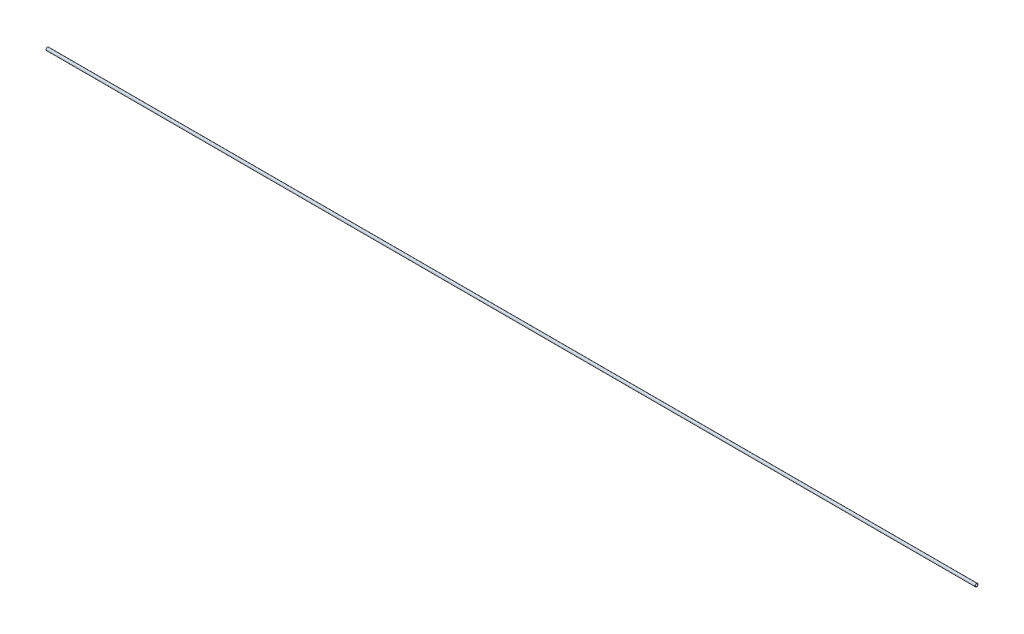
SolidWorks part; units mm, degrees
ref_plane "Front Plane" through (0, 0, 0) normal (0, 0, 1) x (1, 0, 0)
ref_plane "Top Plane" through (0, 0, 0) normal (0, 1, 0) x (1, 0, 0)
ref_plane "Right Plane" through (0, 0, 0) normal (1, 0, 0) x (0, 0, -1)
sketch "Sketch1" plane through (0, 0, 0) normal (1, 0, 0) x (0, 0, -1)
  circle A0 centre (0, 0) radius 1.905
  dimension "D1" = 3.81
extrude "Boss-Extrude1" add sketch "Sketch1" along normal blind 1219.2
sketch "Sketch2" plane through (0, 0, 0) normal (-1, 0, 0) x (0, 0, 1)
  circle A0 centre (0, 0) radius 1.5875
  dimension "D1" = 3.175
extrude "Cut-Extrude1" cut sketch "Sketch2" against normal through all
